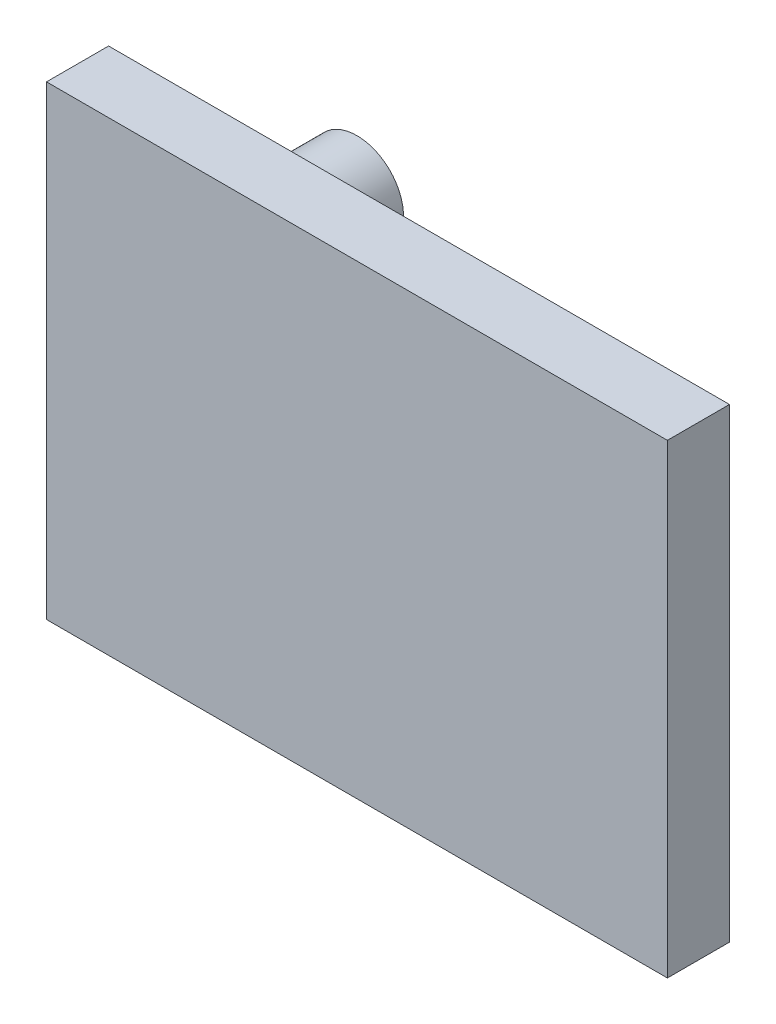
SolidWorks part; units mm, degrees
ref_plane "Front Plane" through (0, 0, 0) normal (0, 0, 1) x (1, 0, 0)
ref_plane "Top Plane" through (0, 0, 0) normal (0, 1, 0) x (1, 0, 0)
ref_plane "Right Plane" through (0, 0, 0) normal (1, 0, 0) x (0, 0, -1)
sketch "Sketch1" plane through (0, 0, 0) normal (0, 0, 1) x (1, 0, 0)
  line L1 (-100, -75) -> (100, -75)
  line L2 (-100, -75) -> (-100, 75)
  line L3 (-100, 75) -> (100, 75)
  line L4 (100, -75) -> (100, 75)
  line L5 (-100, -75) -> (100, 75) construction
  line L6 (-100, 75) -> (100, -75) construction
  point P0 (0, 0)
  dimension "D1" = 200
  dimension "D2" = 150
extrude "Boss-Extrude1" add sketch "Sketch1" along normal blind 20
sketch "Sketch2" plane through (0, 0, 0) normal (0, 0, -1) x (-1, 0, 0)
  line L0 (50, 45) -> (26.5266, 45) construction
  line L1 (50, 45) -> (50, 84.1074) construction
  line L2 (-100, -75) -> (-100, 75) construction
  line L3 (100, -75) -> (-100, -75) construction
  circle A0 centre (-50, -45) radius 10
  circle A1 centre (50, 45) radius 15
  dimension "D1" = 20
  dimension "D2" = 30
  dimension "D3" = 50
  dimension "D4" = 30
  dimension "D5" = 90
  dimension "D6" = 100
extrude "Boss-Extrude2" add sketch "Sketch2" along normal blind 30
